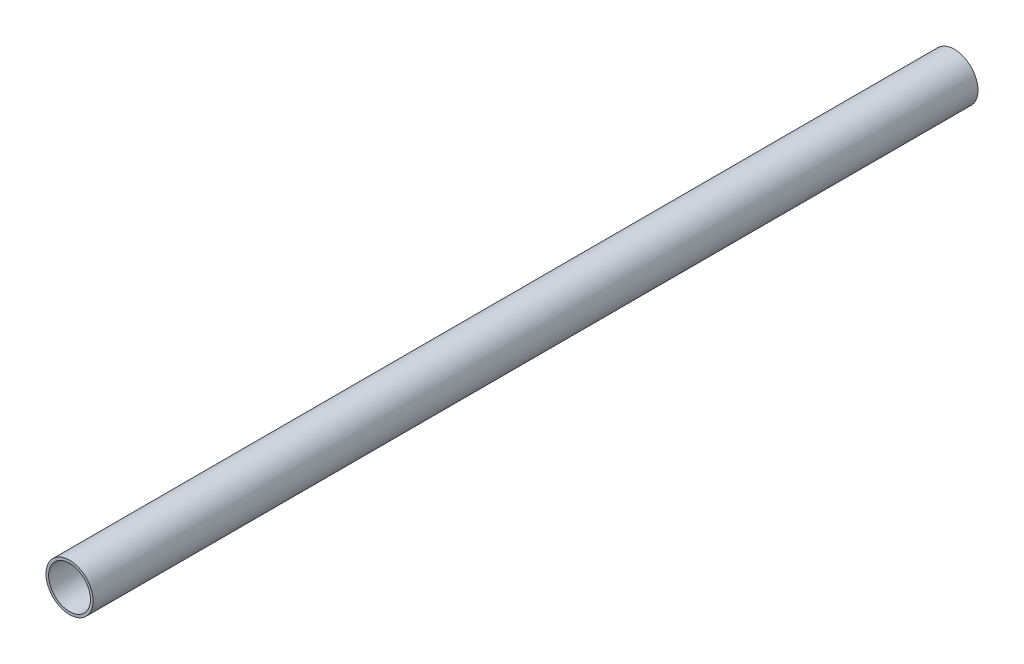
SolidWorks part; units mm, degrees
material "PVC Rigid"
ref_plane "Front Plane" through (0, 0, 0) normal (0, 0, 1) x (1, 0, 0)
ref_plane "Top Plane" through (0, 0, 0) normal (0, 1, 0) x (1, 0, 0)
ref_plane "Right Plane" through (0, 0, 0) normal (1, 0, 0) x (0, 0, -1)
sketch "Sketch1" plane through (0, 0, 0) normal (0, 0, 1) x (1, 0, 0)
  circle A0 centre (0, 0) radius 16.5926
  circle A2 centre (0, 0) radius 14.7257
  dimension "D1" = 33.1851
  dimension "D2" = 1.8669
extrude "Boss-Extrude1" add sketch "Sketch1" along normal blind 622.3
